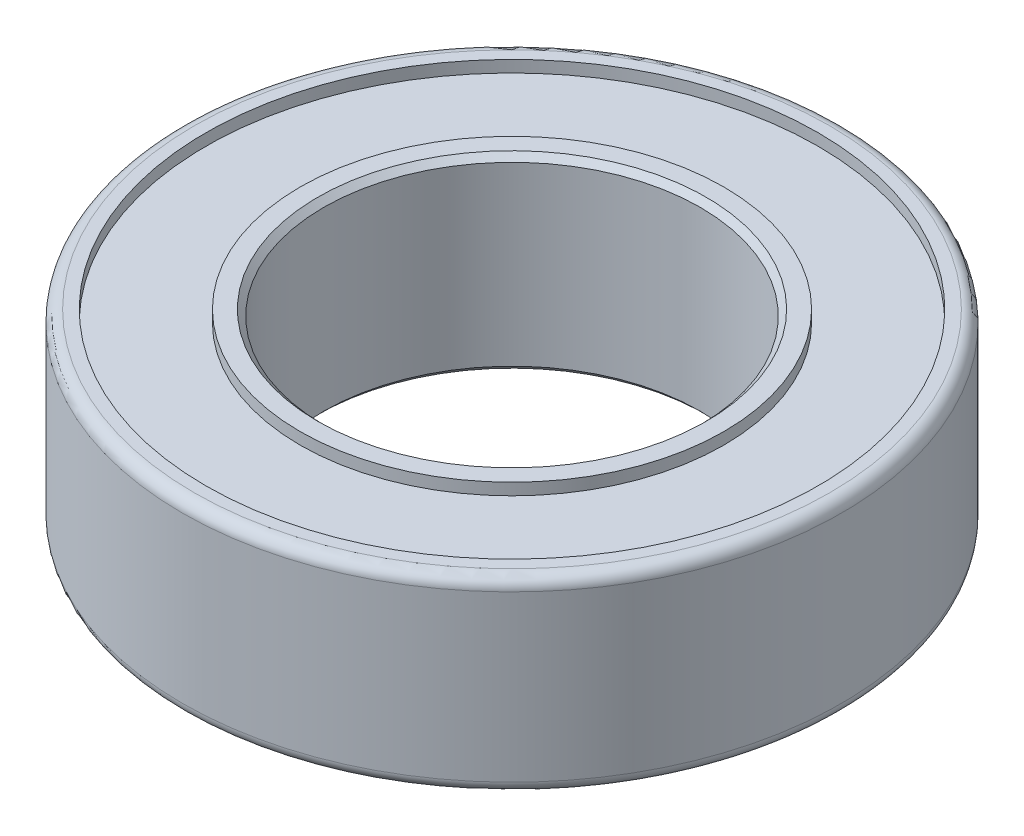
SolidWorks part; units mm, degrees
ref_plane "Front Plane" through (0, 0, 0) normal (0, 0, 1) x (1, 0, 0)
ref_plane "Top Plane" through (0, 0, 0) normal (0, 1, 0) x (1, 0, 0)
ref_plane "Right Plane" through (0, 0, 0) normal (1, 0, 0) x (0, 0, -1)
sketch "Sketch2" plane through (0, 0, 0) normal (0, 1, 0) x (1, 0, 0)
  circle A0 centre (0, 0) radius 4
  circle A1 centre (0, 0) radius 7
  dimension "D1" = 8
  dimension "D2" = 14
extrude "Boss-Extrude1" add sketch "Sketch2" along normal mid plane 4
sketch "Sketch3" plane through (0, 2, 0) normal (0, 1, 0) x (1, 0, 0)
  circle A0 centre (0, 0) radius 4.5
  circle A1 centre (0, 0) radius 6.5
  dimension "D1" = 9
  dimension "D2" = 13
extrude "Cut-Extrude1" cut sketch "Sketch3" against normal blind 0.25
mirror "Mirror1" about plane through (0, 0, 0) normal (0, 1, 0) of "Cut-Extrude1"
fillet "Fillet1" radius 0.25 2 edges at (0, -2, 7) (0, 2, 7)
chamfer "Chamfer1" distance 0.125 angle 45 2 edges at (0, 2, 4) (0, -2, 4)
